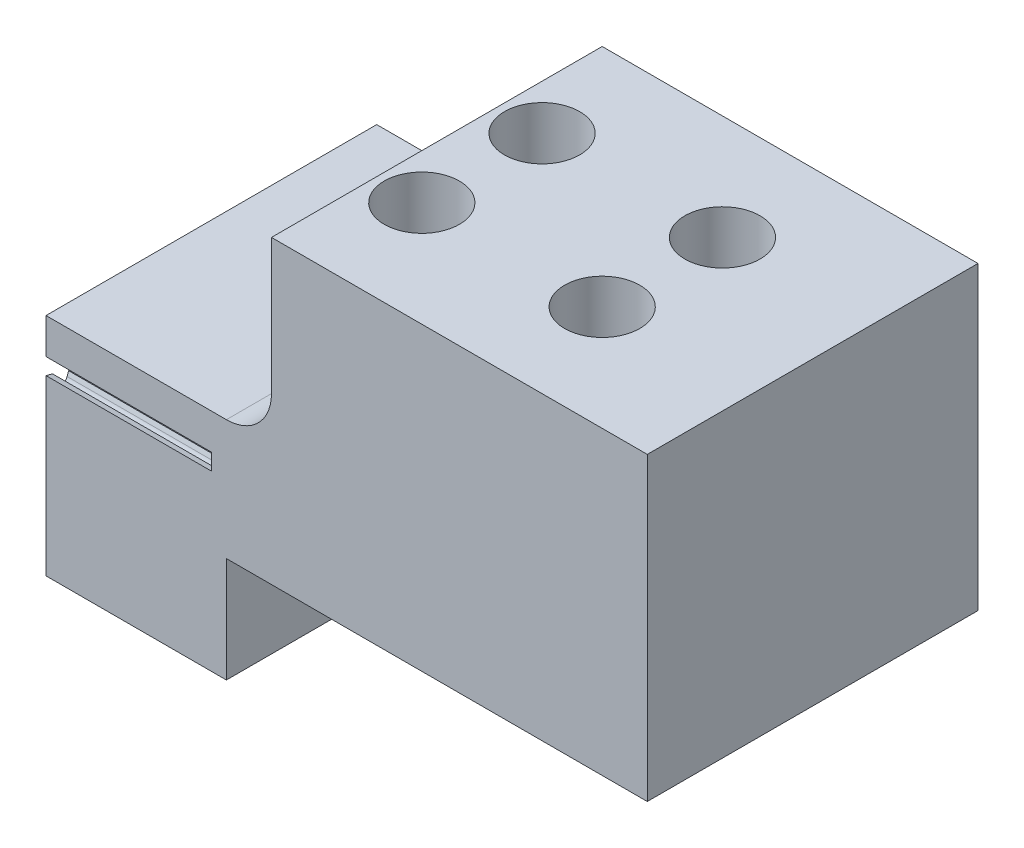
SolidWorks part; units mm, degrees
ref_plane "前视基准面" through (0, 0, 0) normal (0, 0, 1) x (1, 0, 0)
ref_plane "上视基准面" through (0, 0, 0) normal (0, 1, 0) x (1, 0, 0)
ref_plane "右视基准面" through (0, 0, 0) normal (1, 0, 0) x (0, 0, -1)
sketch "草图1" plane through (0, 0, 0) normal (0, 0, 1) x (1, 0, 0)
  line L1 (0, 0) -> (20, 0)
  line L2 (0, 0) -> (0, 40)
  line L3 (0, 40) -> (20, 40)
  line L4 (20, 0) -> (20, 40)
  dimension "D1" = 20
  dimension "D2" = 40
extrude "凸台-拉伸1" add sketch "草图1" along normal blind 30
sketch "草图3" plane through (0, 0, 0) normal (-1, 0, 0) x (0, 0, 1)
  line L0 (2.4208, 14.561) -> (2.4664, 14.8574)
  line L1 (1.5406, 14.6738) -> (1.5712, 14.9721)
  line L4 (0.4512, 15.0436) -> (0.4437, 14.7438)
  line L6 (0, 15.05) -> (0, 16.1115)
  line L134 (14.0938, 6.0136) -> (14.0938, 3.4042)
  line L135 (13.7667, 7.0938) -> (13.5073, 6.9433)
  line L136 (13.2941, 7.8627) -> (13.0426, 7.6992)
  line L137 (12.4086, 8.5971) -> (12.6467, 8.7794)
  line L138 (11.8516, 9.2879) -> (12.0802, 9.482)
  line L139 (11.3216, 10.309) -> (11.1085, 10.0979)
  line L140 (10.6704, 10.9338) -> (10.4683, 10.7122)
  line L141 (9.6283, 11.4212) -> (9.8128, 11.6577)
  line L142 (8.9151, 11.9492) -> (9.0874, 12.1946)
  line L143 (8.1448, 12.8036) -> (7.9918, 12.5456)
  line L144 (7.357, 13.2441) -> (7.2173, 12.9787)
  line L145 (6.2257, 13.4529) -> (6.3446, 13.7283)
  line L146 (5.4024, 13.784) -> (5.5073, 14.065)
  line L147 (4.4415, 14.4166) -> (4.3586, 14.1283)
  line L148 (3.5682, 14.6441) -> (3.4999, 14.3521)
  line L149 (15, 7.0547) -> (15, 0) construction
  line L150 (0, 40) -> (0, 0) construction
  line L151 (30, 0) -> (0, 0) construction
  line L152 (14.0938, 3.4042) -> (15.9062, 3.4042)
  line L153 (26.4318, 14.6441) -> (26.5001, 14.3521)
  line L154 (30, 15.05) -> (30, 16.1115)
  line L155 (29.5488, 15.0436) -> (29.5563, 14.7438)
  line L156 (28.4594, 14.6738) -> (28.4288, 14.9721)
  line L157 (27.5792, 14.561) -> (27.5336, 14.8574)
  line L158 (25.5585, 14.4166) -> (25.6414, 14.1283)
  line L159 (24.5976, 13.784) -> (24.4927, 14.065)
  line L160 (23.7743, 13.4529) -> (23.6554, 13.7283)
  line L161 (22.643, 13.2441) -> (22.7827, 12.9787)
  line L162 (21.8552, 12.8036) -> (22.0082, 12.5456)
  line L163 (21.0849, 11.9492) -> (20.9126, 12.1946)
  line L164 (20.3717, 11.4212) -> (20.1872, 11.6577)
  line L165 (19.3296, 10.9338) -> (19.5317, 10.7122)
  line L166 (18.6784, 10.309) -> (18.8915, 10.0979)
  line L167 (18.1484, 9.2879) -> (17.9198, 9.482)
  line L168 (17.5914, 8.5971) -> (17.3533, 8.7794)
  line L169 (16.7059, 7.8627) -> (16.9574, 7.6992)
  line L170 (16.2333, 7.0938) -> (16.4927, 6.9433)
  line L171 (15.9062, 6.0136) -> (15.9062, 3.4042)
  arc A25 (0, 14.75) -> (15, 3.4042) centre (0, -0.8385) cw construction
  arc A26 (3.4999, 14.3521) -> (2.4208, 14.561) centre (2.9644, 14.4773) cw
  arc A27 (1.5712, 14.9721) -> (2.4664, 14.8574) centre (0, -0.8385) cw
  arc A30 (0.4437, 14.7438) -> (1.5406, 14.6738) centre (0.9935, 14.7299) ccw
  arc A104 (0, 15.05) -> (0.4512, 15.0436) centre (0, -0.8385) cw
  arc A105 (0, 16.1115) -> (15, 7.0547) centre (0, -0.8385) cw
  arc A125 (13.5073, 6.9433) -> (14.0938, 6.0136) centre (13.7834, 6.4676) ccw
  arc A126 (13.7667, 7.0938) -> (13.2941, 7.8627) centre (0, -0.8385) ccw
  arc A127 (13.0426, 7.6992) -> (12.4086, 8.5971) centre (12.7429, 8.1604) cw
  arc A128 (12.6467, 8.7794) -> (12.0802, 9.482) centre (0, -0.8385) ccw
  arc A129 (11.1085, 10.0979) -> (11.8516, 9.2879) centre (11.4956, 9.7072) ccw
  arc A130 (10.6704, 10.9338) -> (11.3216, 10.309) centre (0, -0.8385) cw
  arc A131 (10.4683, 10.7122) -> (9.6283, 11.4212) centre (10.0619, 11.0829) cw
  arc A132 (9.0874, 12.1946) -> (9.8128, 11.6577) centre (0, -0.8385) cw
  arc A133 (7.9918, 12.5456) -> (8.9151, 11.9492) centre (8.4649, 12.2652) ccw
  arc A134 (8.1448, 12.8036) -> (7.357, 13.2441) centre (0, -0.8385) ccw
  arc A135 (7.2173, 12.9787) -> (6.2257, 13.4529) centre (6.7306, 13.2349) cw
  arc A136 (6.3446, 13.7283) -> (5.5073, 14.065) centre (0, -0.8385) ccw
  arc A137 (4.3586, 14.1283) -> (5.4024, 13.784) centre (4.8871, 13.9763) ccw
  arc A138 (4.4415, 14.4166) -> (3.5682, 14.6441) centre (0, -0.8385) ccw
  arc A139 (30, 15.05) -> (29.5488, 15.0436) centre (30, -0.8385) ccw
  arc A140 (29.5563, 14.7438) -> (28.4594, 14.6738) centre (29.0065, 14.7299) cw
  arc A141 (28.4288, 14.9721) -> (27.5336, 14.8574) centre (30, -0.8385) ccw
  arc A142 (26.5001, 14.3521) -> (27.5792, 14.561) centre (27.0356, 14.4773) ccw
  arc A143 (25.5585, 14.4166) -> (26.4318, 14.6441) centre (30, -0.8385) cw
  arc A144 (25.6414, 14.1283) -> (24.5976, 13.784) centre (25.1129, 13.9763) cw
  arc A145 (23.6554, 13.7283) -> (24.4927, 14.065) centre (30, -0.8385) cw
  arc A146 (22.7827, 12.9787) -> (23.7743, 13.4529) centre (23.2694, 13.2349) ccw
  arc A147 (21.8552, 12.8036) -> (22.643, 13.2441) centre (30, -0.8385) cw
  arc A148 (22.0082, 12.5456) -> (21.0849, 11.9492) centre (21.5351, 12.2652) cw
  arc A149 (20.9126, 12.1946) -> (20.1872, 11.6577) centre (30, -0.8385) ccw
  arc A150 (19.5317, 10.7122) -> (20.3717, 11.4212) centre (19.9381, 11.0829) ccw
  arc A151 (19.3296, 10.9338) -> (18.6784, 10.309) centre (30, -0.8385) ccw
  arc A152 (30, 14.75) -> (15, 3.4042) centre (30, -0.8385) ccw construction
  arc A153 (18.8915, 10.0979) -> (18.1484, 9.2879) centre (18.5044, 9.7072) cw
  arc A154 (17.3533, 8.7794) -> (17.9198, 9.482) centre (30, -0.8385) cw
  arc A155 (16.9574, 7.6992) -> (17.5914, 8.5971) centre (17.2571, 8.1604) ccw
  arc A156 (16.2333, 7.0938) -> (16.7059, 7.8627) centre (30, -0.8385) cw
  arc A157 (16.4927, 6.9433) -> (15.9062, 6.0136) centre (16.2166, 6.4676) cw
  arc A158 (30, 16.1115) -> (15, 7.0547) centre (30, -0.8385) ccw
  dimension "D3" = 15.5885
extrude "切除-拉伸1" cut sketch "草图3" against normal blind 11
sketch "草图13" plane through (0, 40, 0) normal (0, 1, 0) x (1, 0, 0)
  line L4 (20, 0) -> (0, 0)
  line L5 (0, 0) -> (0, -30)
  line L6 (0, -30) -> (20, -30)
  line L7 (20, -30) -> (20, 0)
  line L8 (20, 0) -> (0, 0)
  line L9 (0, 0) -> (0, -30)
  line L10 (0, -30) -> (20, -30)
  line L11 (20, -30) -> (20, 0)
  dimension "D1" = 0
extrude "切除-拉伸5" cut sketch "草图13" against normal blind 10
sketch "草图14" plane through (20, 0, 0) normal (1, 0, 0) x (0, 0, -1)
  line L4 (0, 30) -> (-30, 30)
  line L5 (-30, 30) -> (-30, 0)
  line L6 (-30, 0) -> (0, 0)
  line L7 (0, 0) -> (0, 30)
  line L8 (0, 30) -> (-30, 30)
  line L9 (-30, 30) -> (-30, 0)
  line L10 (-30, 0) -> (0, 0)
  line L11 (0, 0) -> (0, 30)
  dimension "D1" = 0
extrude "凸台-拉伸5" add sketch "草图14" along normal blind 20
hole_wizard "M2 间隙孔1" positions "草图17" profile "草图18" hole size "M2" standard "ISO" end condition through all
sketch "草图17" plane through (0, 30, 0) normal (0, 1, 0) x (1, 0, 0)
  line L0 (39.347, -15) -> (-0.653, -15) construction
  line L4 (40, 0) -> (40, -30) construction
  point P0 (18, -11)
  point P2 (30, -11)
  point P18 (18, -19)
  point P19 (30, -19)
  dimension "D1" = 12
  dimension "D2" = 4
  dimension "D3" = 10
sketch "草图18" plane through (18, 30, 11) normal (1, 0, 0) x (0, 0, 1)
  line L0 (0, 0) -> (0, 30)
  line L1 (0, 30) -> (1.2, 30)
  line L2 (1.2, 30) -> (1.2, 0.025)
  line L3 (1.2, 0.025) -> (1.225, 0)
  line L5 (1.225, 0) -> (0, 0)
  line L6 (-1.2, 0.025) -> (-1.225, 0) construction
  line L11 (0, -6.35) -> (0, 107.95) construction
  dimension "通孔孔直径" = 2.4
  dimension "通孔孔深度" = 30
  dimension "近端锥形沉头孔直径" = 2.45
  dimension "近端锥形沉头孔角度" = 90
sketch "草图19" plane through (0, 30, 0) normal (0, 1, 0) x (1, 0, 0)
  circle A0 centre (18, -11) radius 2.5
  circle A1 centre (30, -11) radius 2.5
  circle A2 centre (30, -19) radius 2.5
  circle A3 centre (18, -19) radius 2.5
  dimension "D1" = 5
  dimension "D2" = 5
  dimension "D3" = 5
  dimension "D4" = 5
extrude "切除-拉伸6" cut sketch "草图19" against normal blind 12
sketch "草图20" plane through (40, 0, 0) normal (1, 0, 0) x (0, 0, -1)
  line L0 (-30, 0) -> (0, 0) construction
  line L1 (-30, 30) -> (-26, 30)
  line L2 (-30, 30) -> (-30, 0)
  line L3 (-30, 0) -> (-26, 0)
  line L4 (-26, 30) -> (-26, 0)
  line L6 (0, 30) -> (-4, 30)
  line L7 (0, 30) -> (0, 0)
  line L8 (0, 0) -> (-4, 0)
  line L9 (-4, 30) -> (-4, 0)
  dimension "D1" = 4
  dimension "D2" = 4
extrude "切除-拉伸7" cut sketch "草图20" against normal blind 49
sketch "草图22" plane through (0, 0, 0) normal (0, -1, 0) x (1, 0, 0)
  line L0 (0, 4) -> (40, 4) construction
  line L1 (40, 26) -> (12, 26)
  line L2 (40, 26) -> (40, 4)
  line L3 (40, 4) -> (12, 4)
  line L4 (12, 26) -> (12, 4)
  dimension "D1" = 28
extrude "切除-拉伸8" cut sketch "草图22" against normal blind 10
sketch "草图23" plane through (0, 0, 26) normal (0, 0, 1) x (1, 0, 0)
  line L0 (12, 10) -> (12, 0) construction
  line L1 (0, 0) -> (12, 0)
  line L2 (0, 0) -> (0, 3)
  line L3 (0, 3) -> (12, 3)
  line L4 (12, 0) -> (12, 3)
  dimension "3" = 3
extrude "切除-拉伸9" cut sketch "草图23" against normal through all
sketch "草图24" plane through (0, 0, 0) normal (-1, 0, 0) x (0, 0, 1)
  line L0 (4, 3) -> (26, 3) construction
  line L1 (13.2941, 7.8627) -> (16.7059, 7.8627)
  line L2 (13.2941, 7.8627) -> (13.2941, 3)
  line L3 (13.2941, 3) -> (16.7059, 3)
  line L4 (16.7059, 7.8627) -> (16.7059, 3)
extrude "切除-拉伸10" cut sketch "草图24" against normal up to surface (11 mm away) up to face at (11, 10.8755, 15)
sketch "草图25" plane through (0, 30, 0) normal (0, 1, 0) x (1, 0, 0)
  line L2 (15, -4) -> (0, -4)
  line L3 (0, -4) -> (0, -26)
  line L4 (0, -26) -> (15, -26)
  line L5 (15, -4) -> (15, -26)
  dimension "D1" = 15
extrude "切除-拉伸11" cut sketch "草图25" against normal blind 12
fillet "圆角1" radius 3 1 edges at (15, 18, 15)
